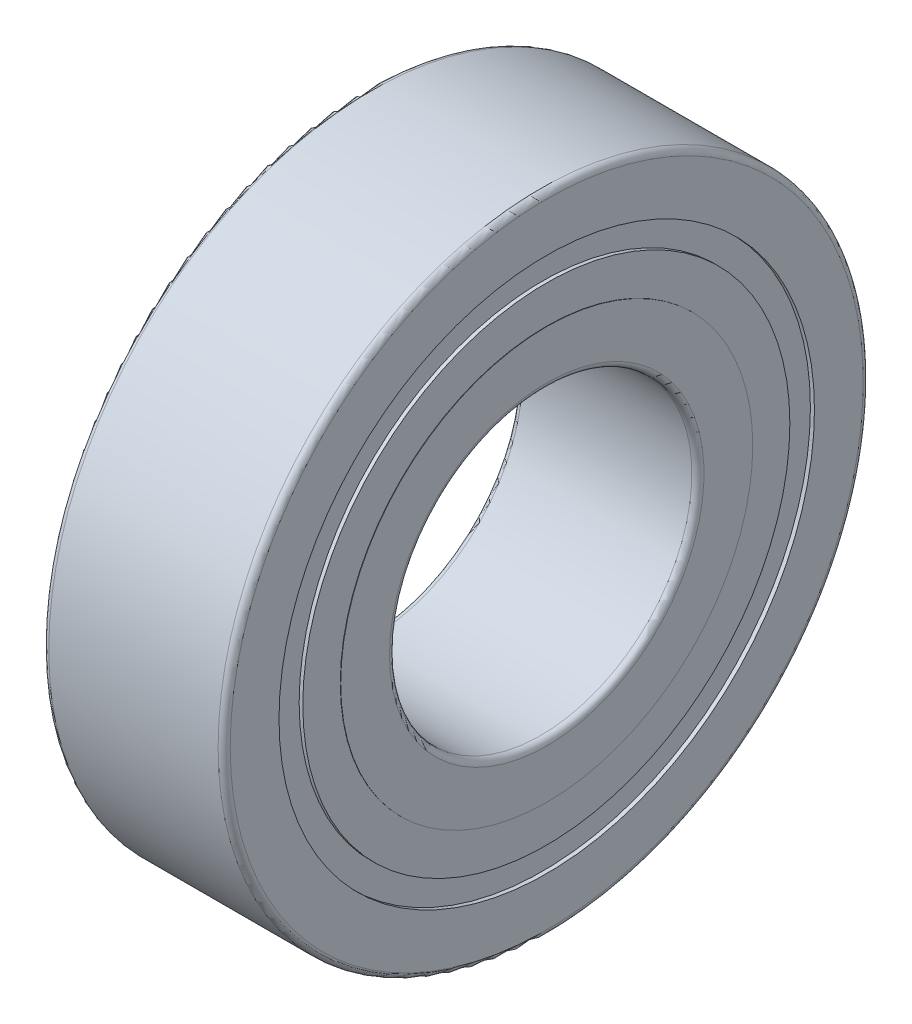
SolidWorks part; units mm, degrees
ref_plane "Front Plane" through (0, 0, 0) normal (0, 0, 1) x (1, 0, 0)
ref_plane "Top Plane" through (0, 0, 0) normal (0, 1, 0) x (1, 0, 0)
ref_plane "Right Plane" through (0, 0, 0) normal (1, 0, 0) x (0, 0, -1)
ref_plane "Plane1" through (0, 0, 0) normal (0, 0, 1) x (1, 0, 0)
sketch "Sketch1" plane through (0, 0, 0) normal (0, 0, 1) x (1, 0, 0)
  line L0 (-4.5, 15.7) -> (-4.5, 7.8)
  line L1 (-4.2, 7.5) -> (4.2, 7.5)
  line L2 (4.5, 7.8) -> (4.5, 15.7)
  line L3 (4.2, 16) -> (-4.2, 16)
  line L4 (50, 0) -> (-50, 0) construction
  arc A0 (-4.5, 7.8) -> (-4.2, 7.5) centre (-4.2, 7.8) ccw
  arc A1 (4.2, 7.5) -> (4.5, 7.8) centre (4.2, 7.8) ccw
  arc A2 (4.5, 15.7) -> (4.2, 16) centre (4.2, 15.7) ccw
  arc A3 (-4.2, 16) -> (-4.5, 15.7) centre (-4.2, 15.7) ccw
revolve "Revolve1" add sketch "Sketch1" angle 360 about L4
ref_plane "Plane2" through (0, 0, 0) normal (0, 0, 1) x (1, 0, 0)
sketch "Sketch2" plane through (0, 0, 0) normal (0, 0, 1) x (1, 0, 0)
  line L0 (-6.3, 7.5) -> (-4.5, 7.5)
  line L1 (-4.5, 7.5) -> (-4.5, 10.22)
  line L2 (-4.5, 10.22) -> (-4.48, 10.22)
  line L3 (-4.48, 10.22) -> (-4.48, 12.08)
  line L4 (-4.48, 12.08) -> (-4.3, 12.08)
  line L5 (-4.3, 12.08) -> (-4.3, 13.28)
  line L6 (-4.3, 13.28) -> (-6.3, 13.28)
  line L7 (-6.3, 13.28) -> (-6.3, 7.5)
  line L8 (50, 0) -> (-50, 0) construction
revolve "Cut-Revolve1" cut sketch "Sketch2" angle 360 about L8
ref_plane "Plane3" through (0, 0, 0) normal (0, 0, 1) x (1, 0, 0)
sketch "Sketch3" plane through (0, 0, 0) normal (0, 0, 1) x (1, 0, 0)
  line L0 (4.3, 13.28) -> (4.3, 12.08)
  line L1 (4.3, 12.08) -> (4.48, 12.08)
  line L2 (4.48, 12.08) -> (4.48, 10.22)
  line L3 (4.48, 10.22) -> (4.5, 10.22)
  line L4 (4.5, 10.22) -> (4.5, 7.5)
  line L5 (4.5, 7.5) -> (6.3, 7.5)
  line L6 (6.3, 7.5) -> (6.3, 13.28)
  line L7 (6.3, 13.28) -> (4.3, 13.28)
  line L8 (50, 0) -> (-50, 0) construction
revolve "Cut-Revolve2" cut sketch "Sketch3" angle 360 about L8
